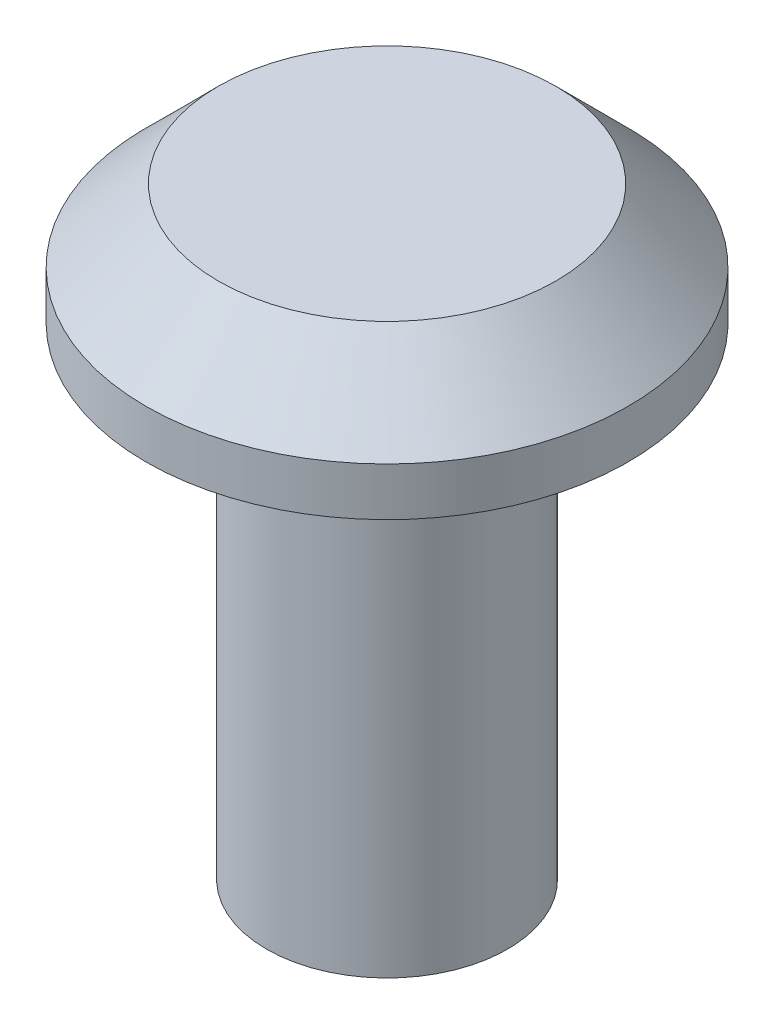
SolidWorks part; units mm, degrees
ref_plane "Piano frontale" through (0, 0, 0) normal (0, 0, 1) x (1, 0, 0)
ref_plane "Piano superiore" through (0, 0, 0) normal (0, 1, 0) x (1, 0, 0)
ref_plane "Piano destro" through (0, 0, 0) normal (1, 0, 0) x (0, 0, -1)
sketch "Schizzo1" plane through (0, 0, 0) normal (0, 1, 0) x (1, 0, 0)
  circle A0 centre (0, 0) radius 1
  dimension "D1" = 2
extrude "Estrusione-Estrusione1" add sketch "Schizzo1" along normal mid plane 0.5 contours A0
chamfer "Smusso1" distance 0.3 angle 45 1 edges at (0, 0.25, 1)
sketch "Schizzo2" plane through (0, -0.25, 0) normal (0, -1, 0) x (1, 0, 0)
  circle A0 centre (0, 0) radius 0.5
  dimension "D1" = 1
extrude "Estrusione-Estrusione2" add sketch "Schizzo2" along normal blind 2 separate body
